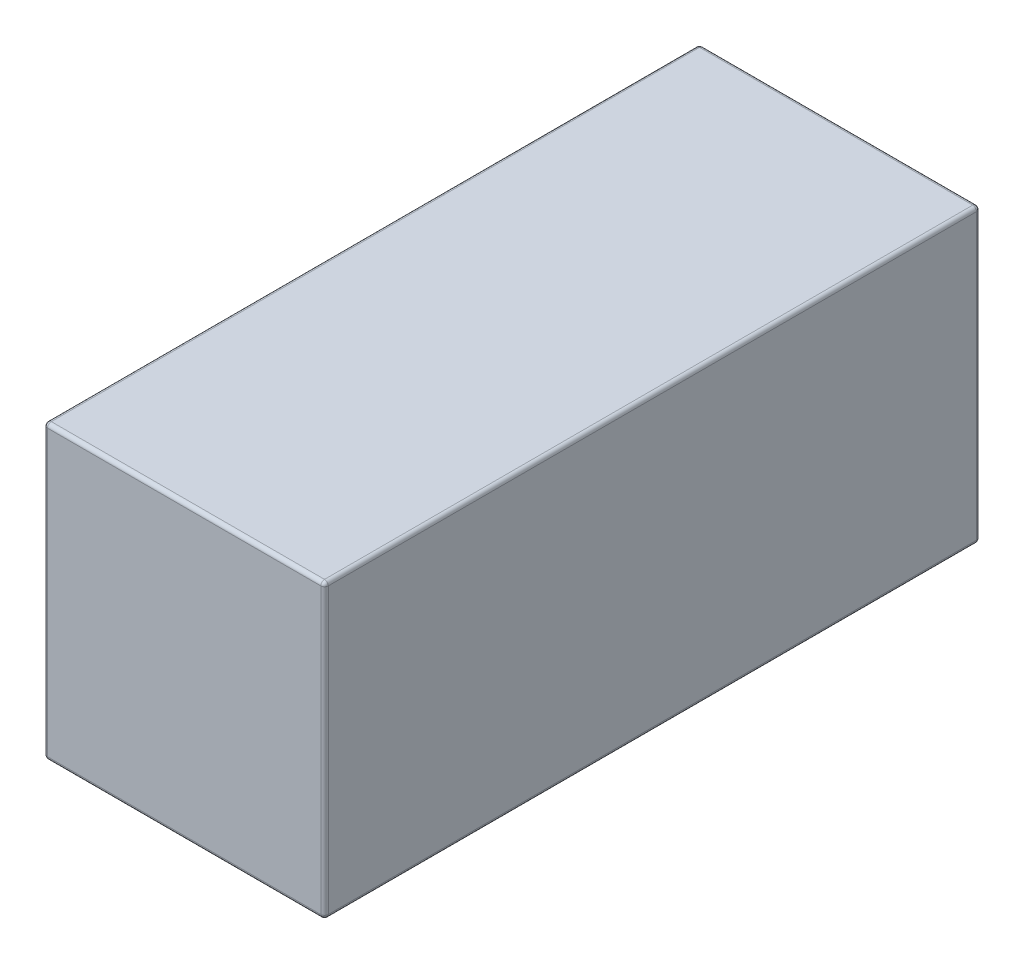
SolidWorks part; units mm, degrees
material "Pine"
ref_plane "Front Plane" through (0, 0, 0) normal (0, 0, 1) x (1, 0, 0)
ref_plane "Top Plane" through (0, 0, 0) normal (0, 1, 0) x (1, 0, 0)
ref_plane "Right Plane" through (0, 0, 0) normal (1, 0, 0) x (0, 0, -1)
sketch "Sketch1" plane through (0, 0, 0) normal (0, 0, 1) x (1, 0, 0)
  line L1 (-18.625, -19.375) -> (18.625, -19.375)
  line L2 (-18.625, -19.375) -> (-18.625, 19.375)
  line L3 (-18.625, 19.375) -> (18.625, 19.375)
  line L4 (18.625, -19.375) -> (18.625, 19.375)
  line L5 (-18.625, -19.375) -> (18.625, 19.375) construction
  line L6 (-18.625, 19.375) -> (18.625, -19.375) construction
  point P0 (0, 0)
  dimension "D1" = 38.75
  dimension "D2" = 37.25
extrude "Boss-Extrude1" add sketch "Sketch1" along normal mid plane 87
fillet "Fillet1" radius 0.5 12 edges at (-18.625, -19.375, 0) (-18.625, 0, -43.5) (0, -19.375, -43.5) (18.625, -19.375, 0) (18.625, 0, -43.5) (0, -19.375, 43.5) (-18.625, 0, 43.5) (18.625, 0, 43.5) (18.625, 19.375, 0) (0, 19.375, 43.5) (-18.625, 19.375, 0) (0, 19.375, -43.5)
